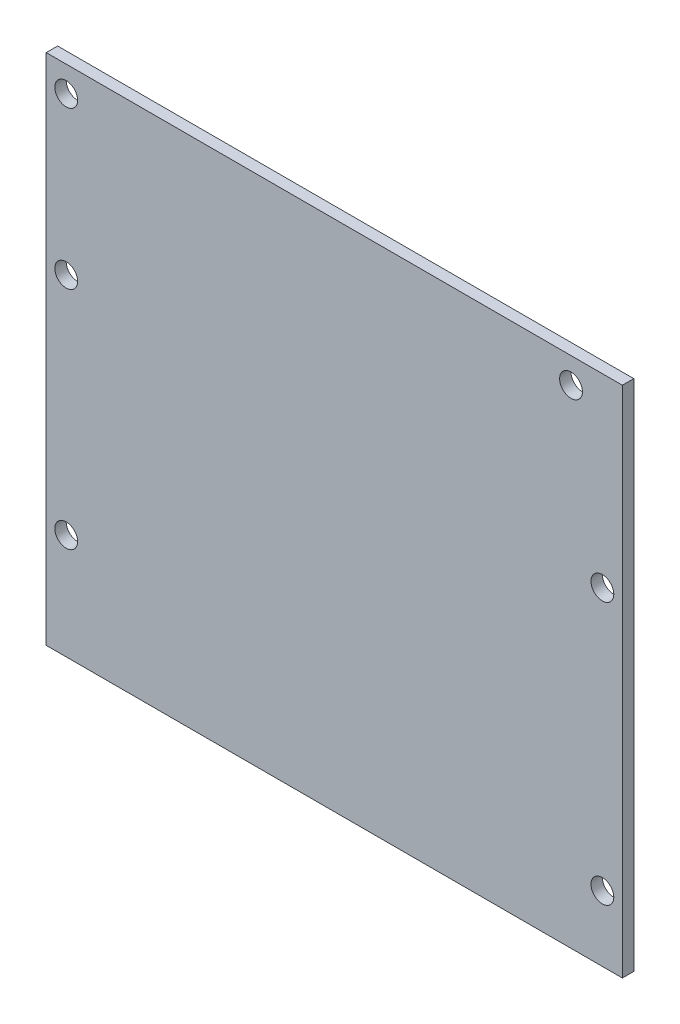
SolidWorks part; units mm, degrees
ref_plane "Plan de face" through (0, 0, 0) normal (0, 0, 1) x (1, 0, 0)
ref_plane "Plan de dessus" through (0, 0, 0) normal (0, 1, 0) x (1, 0, 0)
ref_plane "Plan de droite" through (0, 0, 0) normal (1, 0, 0) x (0, 0, -1)
sketch "Esquisse1" plane through (0, 0, 0) normal (0, 0, 1) x (1, 0, 0)
  line L1 (0, 0) -> (101, 0)
  line L2 (0, 0) -> (0, 90)
  line L3 (0, 90) -> (101, 90)
  line L4 (101, 0) -> (101, 90)
  dimension "D1" = 90
  dimension "D2" = 101
extrude "Main-Sketch" add sketch "Esquisse1" along normal blind 2
sketch "Hole Sketch" plane through (0, 0, 2) normal (0, 0, 1) x (1, 0, 0)
  line L0 (0, 0) -> (101, 0) construction
  line L1 (101, 0) -> (101, 90) construction
  line L2 (0, 90) -> (0, 0) construction
  circle A0 centre (97.5, 11.5) radius 2
  circle A1 centre (97.5, 57.5) radius 2
  circle A2 centre (3.5, 18.5) radius 2
  circle A3 centre (3.5, 58) radius 2
  circle A4 centre (3.5, 85.5) radius 2
  circle A5 centre (92, 85.5) radius 2
  dimension "D1" = 4
  dimension "D2" = 11.5
  dimension "D3" = 3.5
  dimension "D4" = 46
  dimension "D5" = 3.5
  dimension "D6" = 18.5
  dimension "D7" = 58
  dimension "D8" = 85.5
  dimension "D9" = 9
extrude "Holes" cut sketch "Hole Sketch" against normal through all
